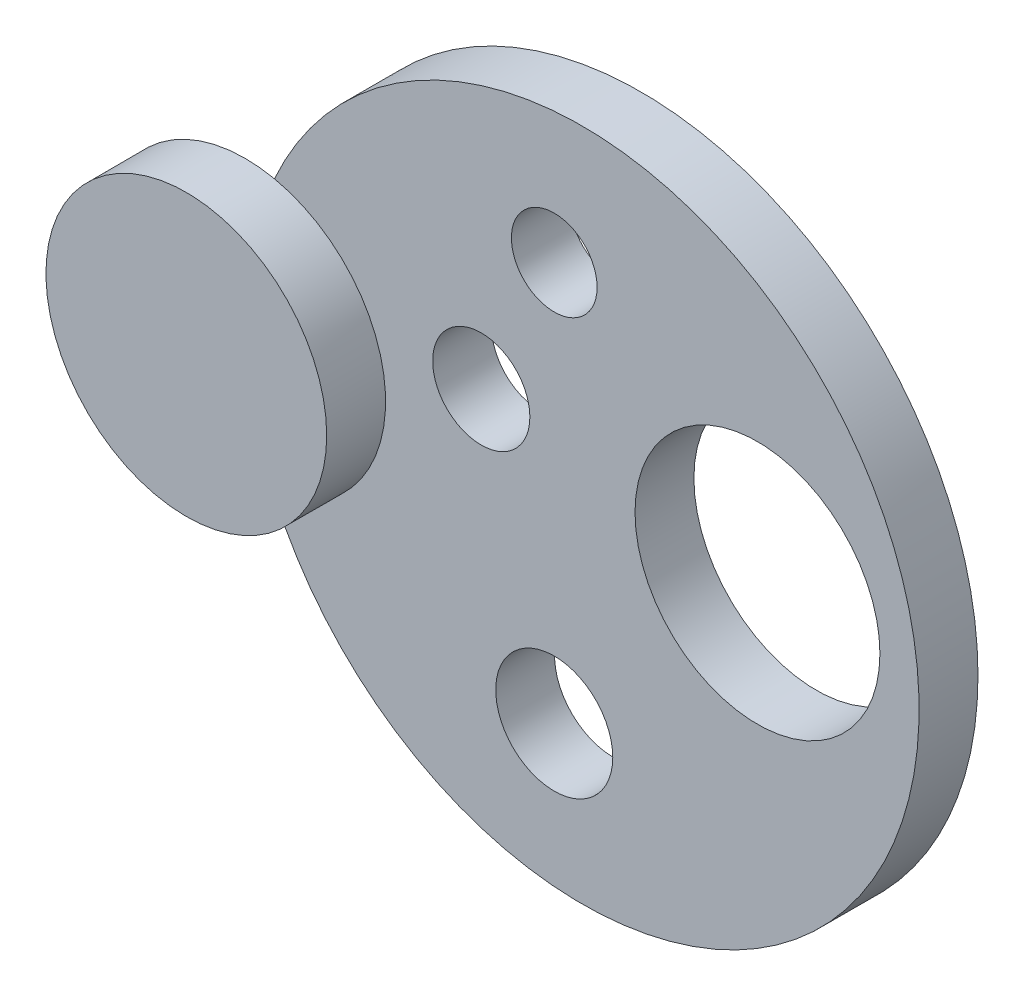
SolidWorks part; units mm, degrees
ref_plane "Alzado" through (0, 0, 0) normal (0, 0, 1) x (1, 0, 0)
ref_plane "Planta" through (0, 0, 0) normal (0, 1, 0) x (1, 0, 0)
ref_plane "Vista lateral" through (0, 0, 0) normal (1, 0, 0) x (0, 0, -1)
sketch "Croquis1" plane through (0, 0, 0) normal (0, 0, 1) x (1, 0, 0)
  circle A0 centre (0, 0) radius 57.2267
  circle A1 centre (-4.742, 34.7594) radius 7.278
  circle A2 centre (-4.742, -33.0459) radius 9.9402
  circle A3 centre (29.7726, 4.8957) radius 20.7966
extrude "Saliente-Extruir1" add sketch "Croquis1" along normal blind 10
sketch "Croquis2" plane through (0, 0, 10) normal (0, 0, 1) x (1, 0, 0)
  circle A0 centre (-57.2267, 0) radius 23.8429
  circle A1 centre (0, 0) radius 57.2267 construction
extrude "Saliente-Extruir2" add sketch "Croquis2" along normal blind 10
sketch "Croquis3" plane through (0, 0, 10) normal (0, 0, 1) x (1, 0, 0)
  circle A0 centre (-17.1358, 9.9686) radius 8.2546
extrude "Cortar-Extruir1" cut sketch "Croquis3" against normal blind 10
